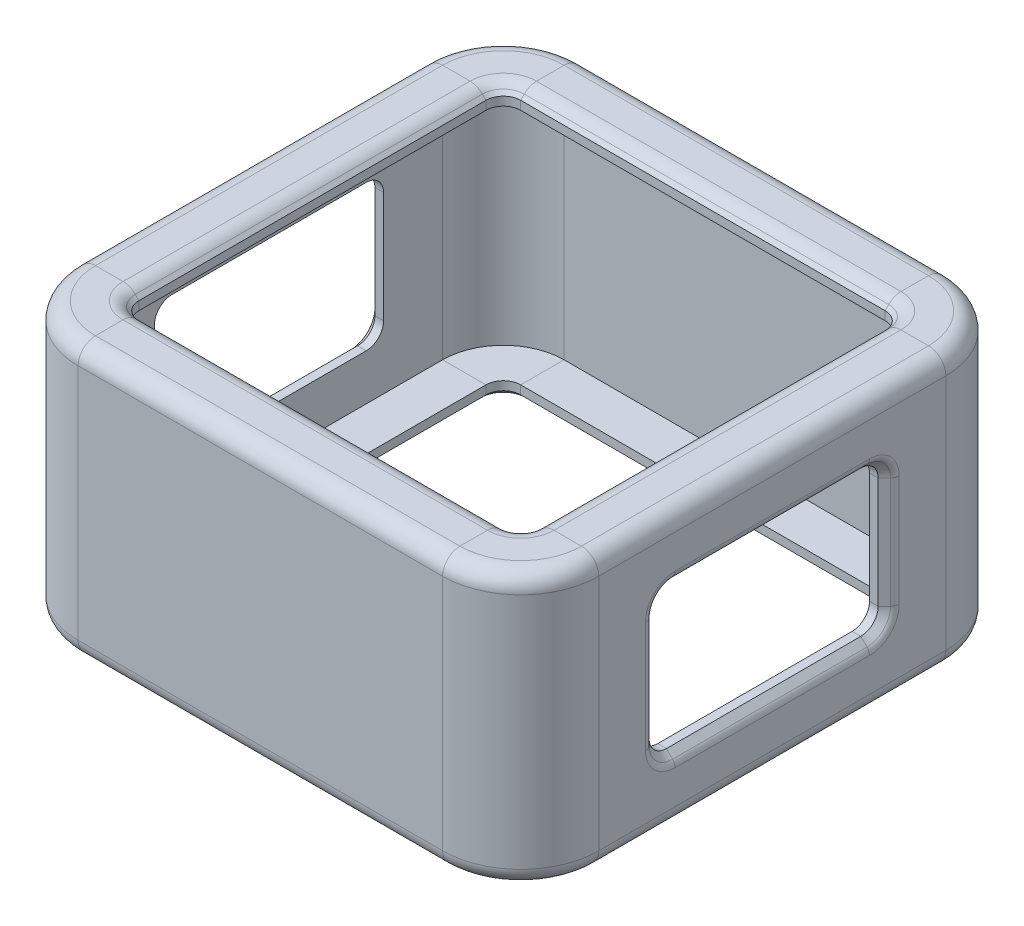
SolidWorks part; units mm, degrees
ref_plane "Front Plane" through (0, 0, 0) normal (0, 0, 1) x (1, 0, 0)
ref_plane "Top Plane" through (0, 0, 0) normal (0, 1, 0) x (1, 0, 0)
ref_plane "Right Plane" through (0, 0, 0) normal (1, 0, 0) x (0, 0, -1)
ref_plane "Plane1 (PCB midplane)" through (0, -0.8, 0) normal (0, 1, 0) x (1, 0, 0)
sketch "Sketch1" plane through (0, 0, 0) normal (0, 0, 1) x (1, 0, 0)
  line L0 (1.5, 4.7502) -> (1.5, 0.0502) construction
  line L1 (1.5, 6.0502) -> (1.5, -0.8)
  line L3 (-1, 6.0502) -> (-1, 6.5502)
  line L4 (1.5, 6.0502) -> (-1, 6.0502)
  line L6 (-1, 6.5502) -> (-0.5, 7.0502)
  line L7 (-0.5, 7.0502) -> (2.5, 7.0502)
  line L8 (2.5, 7.0502) -> (2.5, -0.8)
  line L9 (2.5, -0.8) -> (1.5, -0.8)
  line L10 (1.5, 5.0502) -> (-2, 5.0502) construction
  dimension "D1" = 45
  dimension "D2" = 1
  dimension "D3" = 2.5
  dimension "D4" = 1
  dimension "D5" = 1
sketch "Sketch2" plane through (0, 5.0502, 0) normal (0, 1, 0) x (1, 0, 0)
  line L4 (1.5, 17.5538) -> (1.5, 20)
  line L5 (-2, 23.5) -> (-23, 23.5)
  line L6 (-26.5, 20) -> (-26.5, 17.4932)
  line L7 (-23, -3.5) -> (-2, -3.5)
  line L8 (1.5, 0) -> (1.5, 20)
  line L9 (-2, 23.5) -> (-23, 23.5)
  line L32 (-26.5, 20) -> (-26.5, 0)
  line L33 (0, 17.5538) -> (1.5, 17.5538)
  line L35 (-26.5, 17.4932) -> (-25, 17.4964)
  line L37 (-23, -3.5) -> (-2, -3.5)
  line L38 (-25, 17.4964) -> (-25, 2.5036)
  line L40 (-25, 2.5036) -> (-26.5, 2.5068)
  line L42 (-26.5, 2.5068) -> (-26.5, 0)
  line L44 (1.5, 0) -> (1.5, 2.4462)
  line L46 (1.5, 2.4462) -> (0, 2.4462)
  line L48 (0, 2.4462) -> (0, 17.5538)
  arc A4 (-2, -3.5) -> (1.5, 0) centre (-2, 0) ccw
  arc A5 (1.5, 20) -> (-2, 23.5) centre (-2, 20) ccw
  arc A6 (-23, 23.5) -> (-26.5, 20) centre (-23, 20) ccw
  arc A7 (-23, 23.5) -> (-26.5, 20) centre (-23, 20) ccw
  arc A9 (1.5, 20) -> (-2, 23.5) centre (-2, 20) ccw
  arc A32 (-26.5, 0) -> (-23, -3.5) centre (-23, 0) ccw
  arc A33 (-26.5, 0) -> (-23, -3.5) centre (-23, 0) ccw
  arc A38 (-2, -3.5) -> (1.5, 0) centre (-2, 0) ccw
  point P0 (0, 0)
  dimension "D1" = 0
ref_plane "Plane2 (crossways across PCB)" through (-12.5, 0, 0) normal (-1, 0, 0) x (0, 0, 1)
sweep "Sweep1" add profiles "Sketch1" path "Sketch2"
fillet "Fillet6 (top face)" radius 1 16 edges at (1.182, 7.0502, -23.182) (-0.9393, 7.0502, -21.0607) (-12.5, 7.0502, -24.5) (-12.5, 7.0502, -21.5) (-26.182, 7.0502, -23.182) (-24.0607, 7.0502, -21.0607) (-27.5, 7.0502, -10) (-24.5, 7.0502, -10) (-26.182, 7.0502, 3.182) (-24.0607, 7.0502, 1.0607) (-12.5, 7.0502, 4.5) (-12.5, 7.0502, 1.5) (-0.9393, 7.0502, 1.0607) (1.182, 7.0502, 3.182) (2.5, 7.0502, -10) (-0.5, 7.0502, -10)
sketch "Sketch3" plane through (2.5, 0, 0) normal (1, 0, 0) x (0, 0, -1)
  line L0 (20, -0.8) -> (0, -0.8) construction
  line L1 (5.279, -0.8) -> (13.9832, -0.8) construction
  line L2 (10, 0.8048) -> (10, -2.1258) construction
  line L3 (10, -2.7076) -> (10, 2.2389) construction
  line L6 (7.5, -3.6998) -> (12.5, -3.6998) construction
  line L8 (15.1, -0.4998) -> (15.1, -0.9998) construction
  line L9 (12.5, 2.2002) -> (7.5, 2.2002) construction
  line L12 (16.6, -3.8998) -> (16.6, 3.4002)
  line L14 (3.4, 3.4002) -> (3.4, -3.8998)
  line L40 (16.6, 3.4002) -> (3.4, 3.4002)
  line L41 (3.4, -3.8998) -> (16.6, -3.8998)
  dimension "D1" = 1.5
  dimension "D2" = 0.2
  dimension "D3" = 1.2
extrude "Cut-Extrude1 (side aperture)" cut sketch "Sketch3" against normal up to next
mirror "Mirror6" about plane through (-12.5, 0, 0) normal (-1, 0, 0) of "Cut-Extrude1 (side aperture)"
mirror "Mirror11" about plane through (0, -0.8, 0) normal (0, 1, 0) of "Mirror6", "Cut-Extrude1 (side aperture)", "Fillet6 (top face)", "Sweep1"
fillet "Fillet4 (side aperture inside corners)" radius 1 8 edges at (2, 3.4002, -3.4) (2, 3.4002, -16.6) (-27, 3.4002, -16.6) (-27, -5.0002, -16.6) (-27, -5.0002, -3.4) (-27, 3.4002, -3.4) (2, -5.0002, -3.4) (2, -5.0002, -16.6)
chamfer "Chamfer1 (side aperture)" distance 0.5 angle 45 16 edges at (2.5, -0.8, -16.6) (2.5, 3.1073, -16.3071) (2.5, 3.4002, -10) (2.5, 3.1073, -3.6929) (2.5, -0.8, -3.4) (-27.5, -0.8, -3.4) (-27.5, 3.4002, -10) (-27.5, -0.8, -16.6) (-27.5, -4.7073, -3.6929) (-27.5, 3.1073, -3.6929) (-27.5, -5.0002, -10) (-27.5, -4.7073, -16.3071) (-27.5, 3.1073, -16.3071) (2.5, -5.0002, -10) (2.5, -4.7073, -16.3071) (2.5, -4.7073, -3.6929)
fillet "Fillet5 (side aperture)" radius 0.5 16 edges at (2.5, -0.8, -2.9) (2.5, 3.4609, -3.3393) (2.5, 3.9002, -10) (2.5, 3.4609, -16.6607) (2.5, -0.8, -17.1) (-27.5, -0.8, -2.9) (-27.5, 3.9002, -10) (-27.5, -0.8, -17.1) (-27.5, -5.0609, -16.6607) (-27.5, -5.5002, -10) (-27.5, -5.0609, -3.3393) (-27.5, 3.4609, -3.3393) (-27.5, 3.4609, -16.6607) (2.5, -5.0609, -3.3393) (2.5, -5.5002, -10) (2.5, -5.0609, -16.6607)
